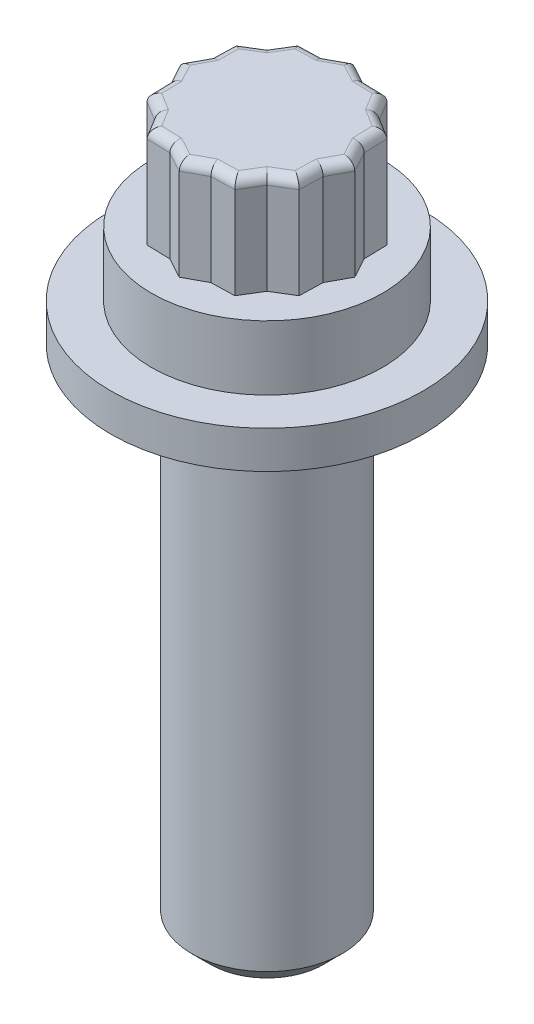
SolidWorks part; units mm, degrees
material "AISI 304"
ref_plane "Front Plane" through (0, 0, 0) normal (0, 0, 1) x (1, 0, 0)
ref_plane "Top Plane" through (0, 0, 0) normal (0, 1, 0) x (1, 0, 0)
ref_plane "Right Plane" through (0, 0, 0) normal (1, 0, 0) x (0, 0, -1)
sketch "Sketch8" plane through (0, 0, 0) normal (0, 1, 0) x (1, 0, 0)
  circle A0 centre (0, 0) radius 6.35
  circle A1 centre (0, 0) radius 3.429
  dimension "D1" = 12.7
  dimension "D2" = 6.858
extrude "Washer" add sketch "Sketch8" along normal blind 1.524 separate body
sketch "Sketch9" plane through (0, 1.524, 0) normal (0, 1, 0) x (1, 0, 0)
  circle A0 centre (0, 0) radius 3.0607
  dimension "D1" = 6.1214
extrude "Boss-Extrude4" add sketch "Sketch9" against normal blind 22.225 separate body
cosmetic thread "Cosmetic Thread2" parameters "D2"=5.8674
sketch "Sketch10" plane through (0, 1.524, 0) normal (0, 1, 0) x (1, 0, 0)
  circle A0 centre (0, 0) radius 4.699
  dimension "D1" = 9.398
extrude "Boss-Extrude5" add sketch "Sketch10" along normal blind 6.731 separate body
sketch "Sketch11" plane through (0, 8.255, 0) normal (0, 1, 0) x (1, 0, 0)
  line L0 (0, 3.5687) -> (-0.8349, 3.1159)
  line L1 (-0.8349, 3.1159) -> (-1.7844, 3.0906)
  line L2 (-1.7844, 3.0906) -> (-2.281, 2.281)
  line L3 (-2.281, 2.281) -> (-3.0906, 1.7844)
  line L4 (-3.0906, 1.7844) -> (-3.1159, 0.8349)
  line L5 (-3.1159, 0.8349) -> (-3.5687, 0)
  line L6 (-3.5687, 0) -> (-3.1159, -0.8349)
  line L7 (-3.1159, -0.8349) -> (-3.0906, -1.7844)
  line L8 (-3.0906, -1.7844) -> (-2.281, -2.281)
  line L9 (-2.281, -2.281) -> (-1.7844, -3.0906)
  line L10 (-1.7844, -3.0906) -> (-0.8349, -3.1159)
  line L11 (-0.8349, -3.1159) -> (0, -3.5687)
  line L12 (0, -3.5687) -> (0.8349, -3.1159)
  line L13 (0.8349, -3.1159) -> (1.7844, -3.0906)
  line L14 (1.7844, -3.0906) -> (2.281, -2.281)
  line L15 (2.281, -2.281) -> (3.0906, -1.7844)
  line L16 (3.0906, -1.7844) -> (3.1159, -0.8349)
  line L17 (3.1159, -0.8349) -> (3.5687, 0)
  line L18 (1.7844, 3.0906) -> (2.281, 2.281)
  line L19 (2.281, 2.281) -> (3.0906, 1.7844)
  line L20 (1.7844, 3.0906) -> (0.8349, 3.1159)
  line L21 (0.8349, 3.1159) -> (0, 3.5687)
  line L22 (3.0906, 1.7844) -> (3.1159, 0.8349)
  line L23 (3.1159, 0.8349) -> (3.5687, 0)
  circle A0 centre (0, 0) radius 3.2258 construction
  circle A1 centre (0, 0) radius 3.5687 construction
  circle A2 centre (0, 0) radius 4.699
  circle A3 centre (0, 0) radius 4.699 construction
  dimension "D1" = 7.1374
  dimension "D2" = 6.4516
extrude "Cut-Extrude2" cut sketch "Sketch11" against normal blind 4.1148
combine bodies "Combine1" operation type add bodies to combine 141 149
fillet "Fillet5" radius 0.381 24 edges at (0.4174, 8.255, -3.3423) (1.3096, 8.255, -3.1032) (2.0327, 8.255, -2.6858) (2.6858, 8.255, -2.0327) (3.1032, 8.255, -1.3096) (3.3423, 8.255, -0.4174) (3.3423, 8.255, 0.4174) (3.1032, 8.255, 1.3096) (2.6858, 8.255, 2.0327) (2.0327, 8.255, 2.6858) (1.3096, 8.255, 3.1032) (0.4174, 8.255, 3.3423) (-0.4174, 8.255, 3.3423) (-1.3096, 8.255, 3.1032) (-2.0327, 8.255, 2.6858) (-2.6858, 8.255, 2.0327) (-3.1032, 8.255, 1.3096) (-3.3423, 8.255, 0.4174) (-3.3423, 8.255, -0.4174) (-3.1032, 8.255, -1.3096) (-2.6858, 8.255, -2.0327) (-2.0327, 8.255, -2.6858) (-1.3096, 8.255, -3.1032) (-0.4174, 8.255, -3.3423)
chamfer "Chamfer1" distance 0.762 angle 45 1 edges at (0, -20.701, 3.0607)
equation "\"D2@Cosmetic Thread2\"=\"D1@Sketch9\"-.01"
